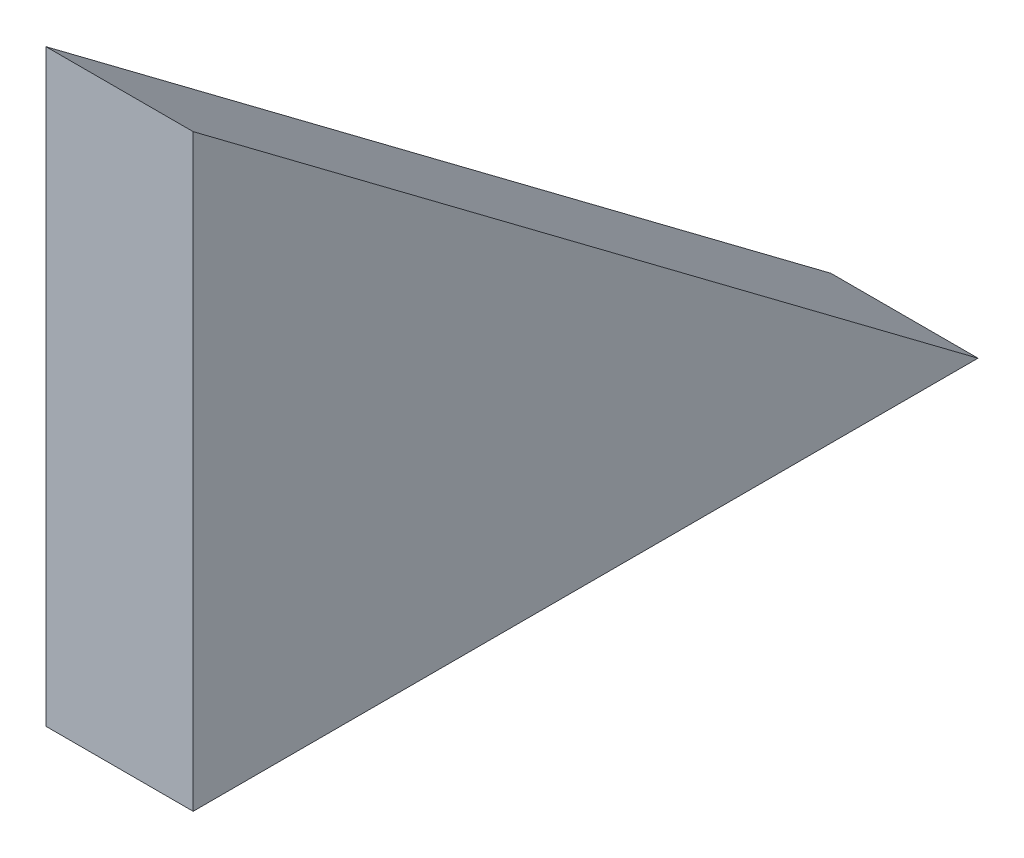
SolidWorks part; units mm, degrees
material "Oak"
ref_plane "Front Plane" through (0, 0, 0) normal (0, 0, 1) x (1, 0, 0)
ref_plane "Top Plane" through (0, 0, 0) normal (0, 1, 0) x (1, 0, 0)
ref_plane "Right Plane" through (0, 0, 0) normal (1, 0, 0) x (0, 0, -1)
sketch "Sketch1" plane through (0, 0, 0) normal (1, 0, 0) x (0, 0, -1)
  line L0 (0, 0) -> (0, 76.2)
  line L1 (0, 76.2) -> (101.6, 0)
  line L2 (101.6, 0) -> (0, 0)
  dimension "D1" = 101.6
  dimension "D2" = 76.2
extrude "Boss-Extrude1" add sketch "Sketch1" along normal mid plane 19.05
